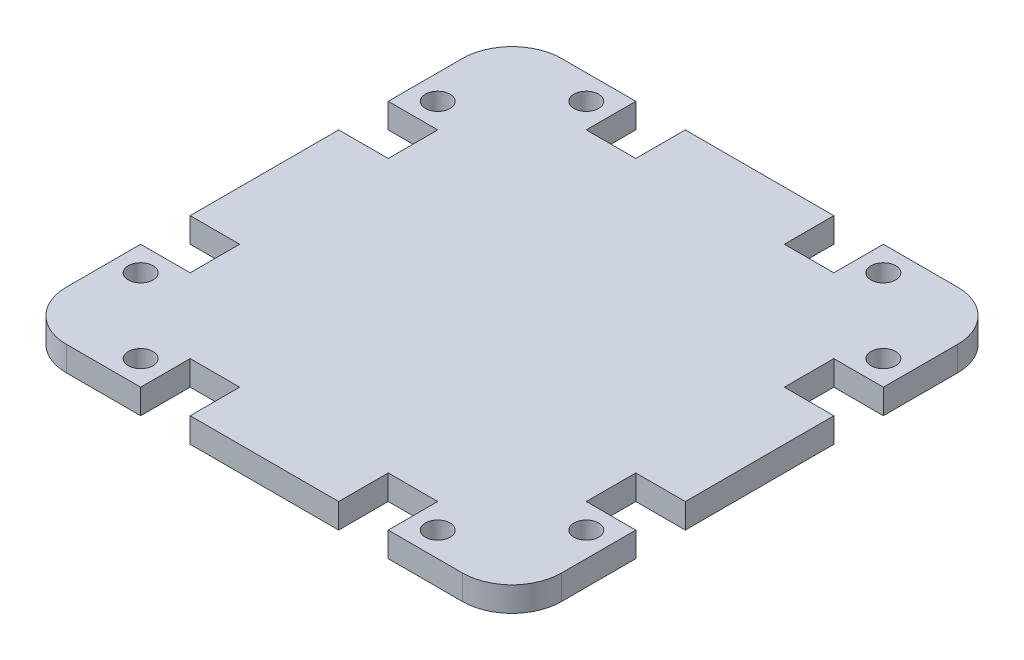
SolidWorks part; units mm, degrees
ref_plane "Front Plane" through (0, 0, 0) normal (0, 0, 1) x (1, 0, 0)
ref_plane "Top Plane" through (0, 0, 0) normal (0, 1, 0) x (1, 0, 0)
ref_plane "Right Plane" through (0, 0, 0) normal (1, 0, 0) x (0, 0, -1)
sketch "Sketch1" plane through (0, 0, 0) normal (0, 1, 0) x (1, 0, 0)
  line L0 (-50, 50) -> (-25, 50) construction
  line L1 (40, -50) -> (-40, -50)
  line L2 (50, -40) -> (50, 40)
  line L3 (40, 50) -> (-40, 50)
  line L4 (-50, -40) -> (-50, 40)
  line L5 (50, -50) -> (-50, 50) construction
  line L6 (50, 50) -> (-50, -50) construction
  line L7 (50, 50) -> (6.5039, 50) construction
  line L8 (0, -1000) -> (0, 49000) construction
  line L9 (-25, 50) -> (-15, 50)
  line L10 (-25, 50) -> (-25, 40)
  line L11 (-25, 40) -> (-15, 40)
  line L12 (-15, 50) -> (-15, 40)
  line L13 (25, 40) -> (15, 40)
  line L14 (15, 50) -> (15, 40)
  line L15 (25, 50) -> (15, 50)
  line L16 (25, 50) -> (25, 40)
  line L17 (50, 25) -> (40, 25)
  line L18 (50, 25) -> (50, 15)
  line L19 (50, 15) -> (40, 15)
  line L20 (40, 25) -> (40, 15)
  line L21 (40, -25) -> (40, -15)
  line L22 (50, -15) -> (40, -15)
  line L23 (50, -25) -> (50, -15)
  line L24 (50, -25) -> (40, -25)
  line L25 (25, -50) -> (25, -40)
  line L26 (25, -50) -> (15, -50)
  line L27 (15, -50) -> (15, -40)
  line L28 (25, -40) -> (15, -40)
  line L29 (-25, -40) -> (-15, -40)
  line L30 (-15, -50) -> (-15, -40)
  line L31 (-25, -50) -> (-15, -50)
  line L32 (-25, -50) -> (-25, -40)
  line L33 (-50, -25) -> (-40, -25)
  line L34 (-50, -25) -> (-50, -15)
  line L35 (-50, -15) -> (-40, -15)
  line L36 (-40, -25) -> (-40, -15)
  line L37 (-40, 25) -> (-40, 15)
  line L38 (-50, 15) -> (-40, 15)
  line L39 (-50, 25) -> (-50, 15)
  line L40 (-50, 25) -> (-40, 25)
  line L41 (50, 50) -> (30, 50)
  line L42 (30, 50) -> (30, 45) construction
  circle A0 centre (30, 45) radius 2.5
  circle A1 centre (45, 30) radius 2.5
  circle A2 centre (45, -30) radius 2.5
  circle A3 centre (30, -45) radius 2.5
  circle A4 centre (-30, -45) radius 2.5
  circle A5 centre (-45, -30) radius 2.5
  circle A6 centre (-45, 30) radius 2.5
  circle A7 centre (-30, 45) radius 2.5
  arc A8 (40, -50) -> (50, -40) centre (40, -40) ccw
  arc A9 (50, 40) -> (40, 50) centre (40, 40) ccw
  arc A10 (-40, 50) -> (-50, 40) centre (-40, 40) ccw
  arc A11 (-40, -50) -> (-50, -40) centre (-40, -40) cw
  point P0 (0, 0)
  point P44 (0, 0)
  point P62 (0, 0)
  dimension "D7" = 20
  dimension "D9" = 10
  dimension "D1" = 10
  dimension "D2" = 10
  dimension "D3" = 100
  dimension "D4" = 100
  dimension "D5" = 25
  dimension "D6" = 4
  dimension "D8" = 4
extrude "Boss-Extrude1" add sketch "Sketch1" along normal blind 5 contours L4 L40 L37 L38 L35 L36 L33 L1 L32 L29 L30 L27 L28 L25 L2 L24 L21 L22 L19 L20 L17 L3 L16 L13 L14 L12 L11 L10 A5 A4 A1 A0 A2 A3 A6
